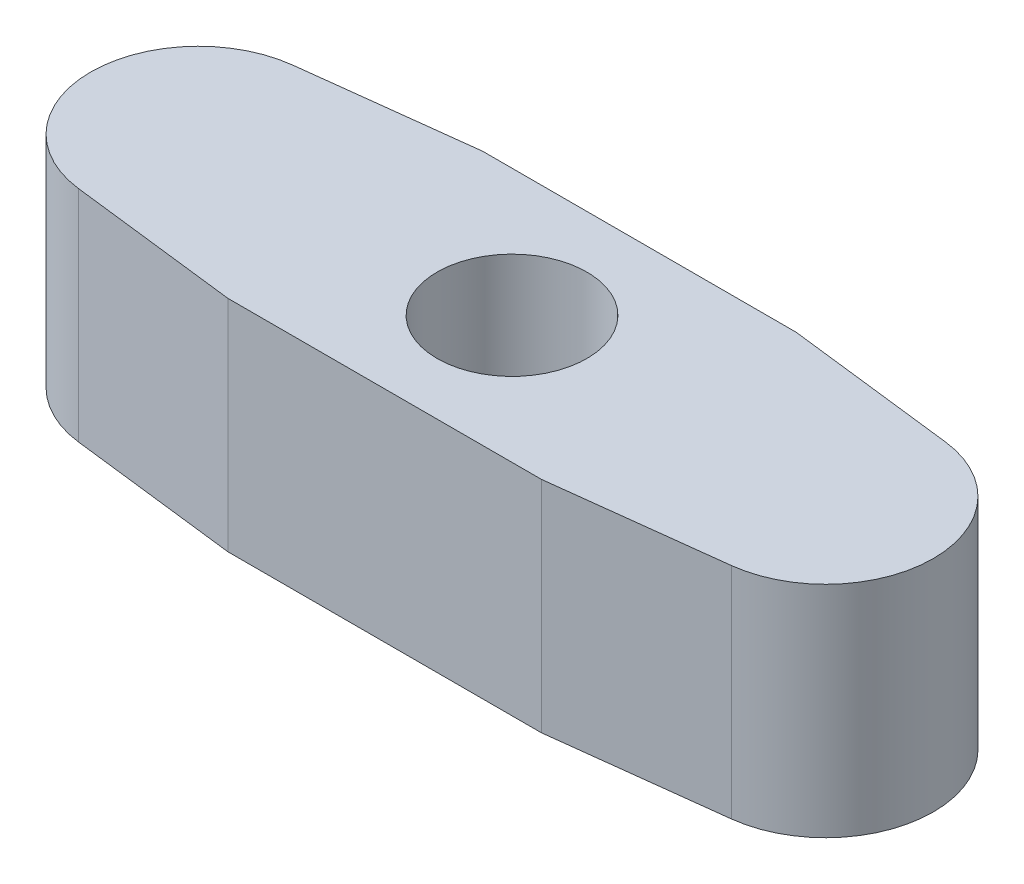
SolidWorks part; units mm, degrees
ref_plane "Front Plane" through (0, 0, 0) normal (0, 0, 1) x (1, 0, 0)
ref_plane "Top Plane" through (0, 0, 0) normal (0, 1, 0) x (1, 0, 0)
ref_plane "Right Plane" through (0, 0, 0) normal (1, 0, 0) x (0, 0, -1)
sketch "Sketch2" plane through (0, 0, 0) normal (0, 1, 0) x (1, 0, 0)
  line L0 (-8.3278, -2.7304) -> (-4, -3.25)
  line L1 (-8.3278, 2.7304) -> (-4, 3.25)
  line L2 (8.3278, -2.7304) -> (4, -3.25)
  line L3 (-4, -3.25) -> (4, -3.25)
  line L4 (-4, -3.25) -> (-4, 3.25)
  line L5 (-4, 3.25) -> (4, 3.25)
  line L6 (4, -3.25) -> (4, 3.25)
  line L7 (-4, -3.25) -> (4, 3.25) construction
  line L8 (-4, 3.25) -> (4, -3.25) construction
  line L11 (8.3278, 2.7304) -> (4, 3.25)
  line L12 (4, 3.25) -> (4.0122, 3.2748)
  line L13 (0, 0) -> (-8, 0) construction
  line L14 (0, 0) -> (8, 0) construction
  circle A0 centre (0, 0) radius 2
  circle A1 centre (-8, 0) radius 2.75
  circle A2 centre (8, 0) radius 2.75
  point P2 (-0.8628, 2.9614)
  point P27 (-0.8669, 2.9614)
  dimension "D4" = 5.5
  dimension "D1" = 4
  dimension "D6" = 6.5
  dimension "D7" = 8
  dimension "D2" = 8
sketch "Sketch4" plane through (0, 0, 0) normal (0, 1, 0) x (1, 0, 0)
  line L2 (-8.3278, 2.7304) -> (-4, 3.25) construction
  line L3 (8.3278, 2.7304) -> (4, 3.25) construction
  line L4 (-4, -3.25) -> (-8.3278, -2.7304)
  line L5 (-4, -3.25) -> (4, -3.25)
  line L6 (4, -3.25) -> (8.3278, -2.7304)
  line L7 (-4, 3.25) -> (-8.3278, 2.7304)
  line L9 (4, 3.25) -> (8.3278, 2.7304)
  line L10 (-4, 3.25) -> (4, 3.25)
  arc A0 (-8.3278, -2.7304) -> (-8.3278, 2.7304) centre (-8, 0) cw
  arc A1 (8.3278, -2.7304) -> (8.3278, 2.7304) centre (8, 0) ccw
  circle A2 centre (0, 0) radius 1.9114
extrude "Boss-Extrude1" add sketch "Sketch4" along normal blind 5.6
